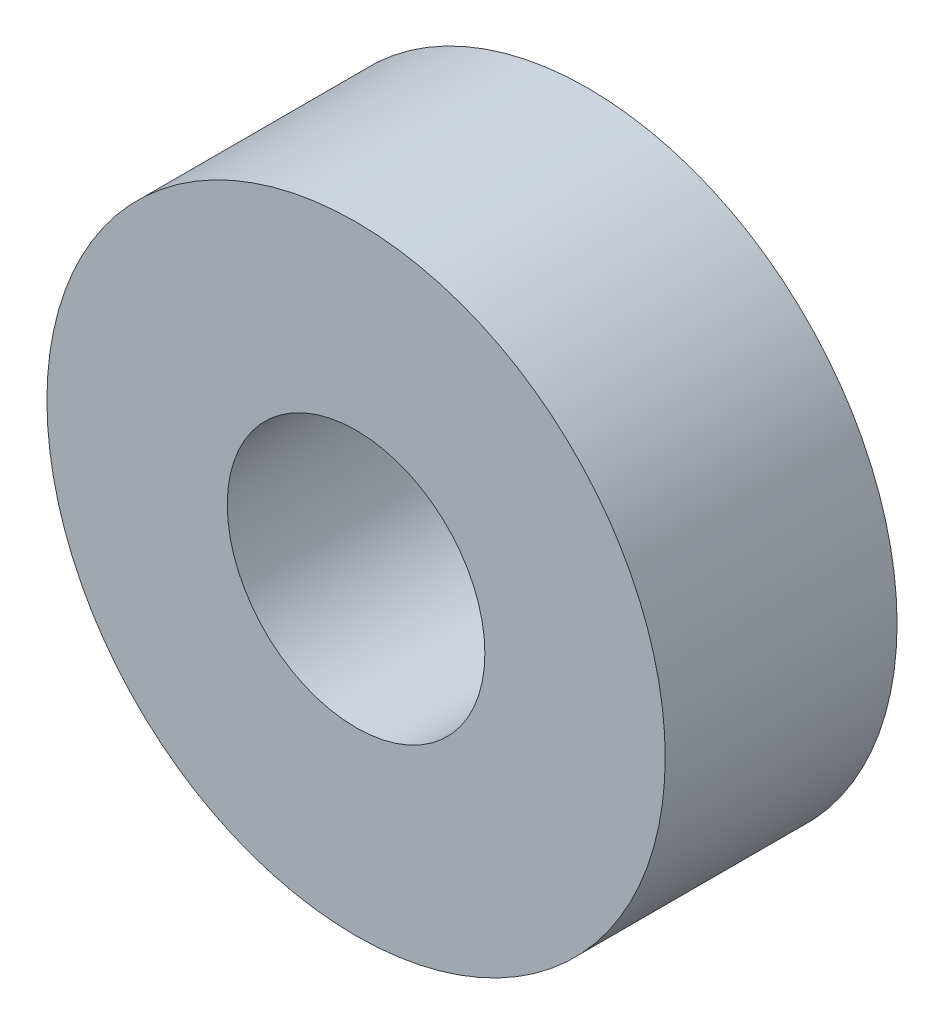
SolidWorks part; units mm, degrees
material "AISI 304"
ref_plane "前视基准面" through (0, 0, 0) normal (0, 0, 1) x (1, 0, 0)
ref_plane "上视基准面" through (0, 0, 0) normal (0, 1, 0) x (1, 0, 0)
ref_plane "右视基准面" through (0, 0, 0) normal (1, 0, 0) x (0, 0, -1)
sketch "草图1" plane through (0, 0, 0) normal (0, 0, 1) x (1, 0, 0)
  circle A0 centre (0, 0) radius 2.5
  circle A1 centre (0, 0) radius 6
  dimension "D1" = 5
  dimension "D2" = 12
extrude "凸台-拉伸1" add sketch "草图1" along normal blind 4.5
